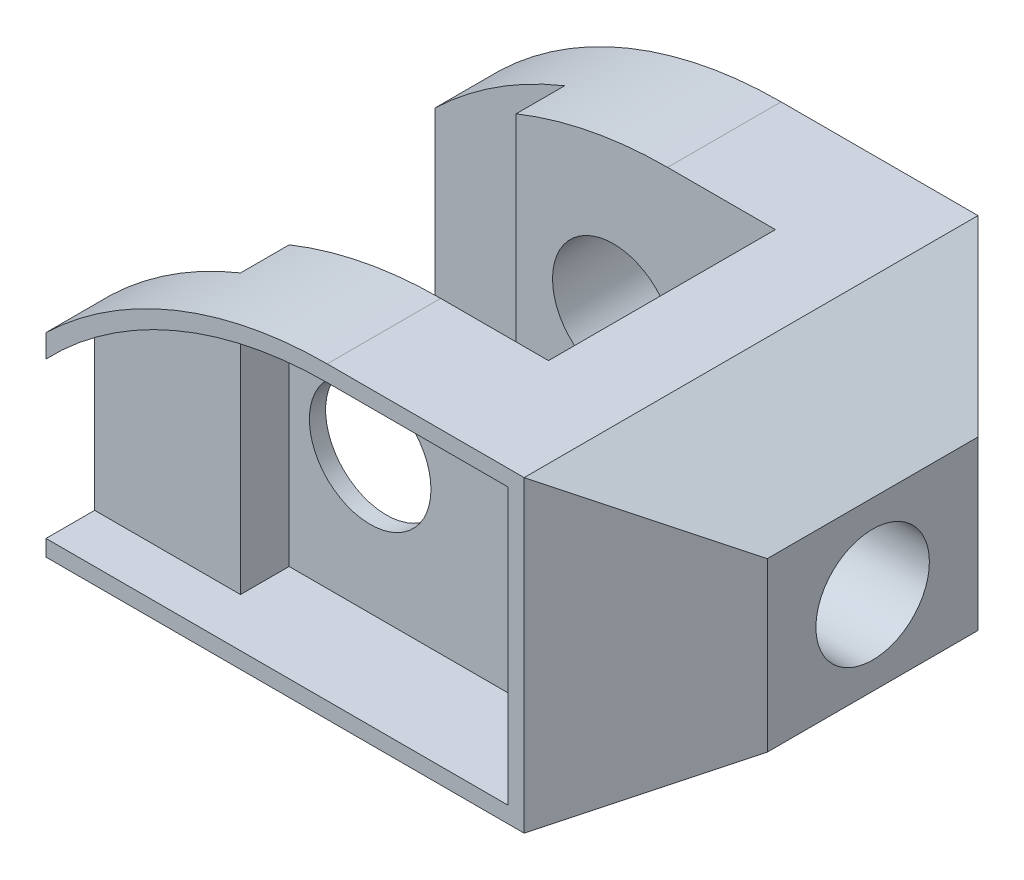
SolidWorks part; units mm, degrees
material "1060 Alloy"
ref_plane "Front Plane" through (0, 0, 0) normal (0, 0, 1) x (1, 0, 0)
ref_plane "Top Plane" through (0, 0, 0) normal (0, 1, 0) x (1, 0, 0)
ref_plane "Right Plane" through (0, 0, 0) normal (1, 0, 0) x (0, 0, -1)
sketch "Sketch1" plane through (0, 0, 0) normal (0, 0, 1) x (1, 0, 0)
  line L0 (-28, -19) -> (31, -19)
  line L1 (-28, -19) -> (-28, 5)
  line L2 (6.6987, 19) -> (31, 19)
  line L3 (0, 0) -> (0, 50000) construction
  line L4 (31, 19) -> (46, 10.3397)
  line L5 (31, -19) -> (46, -10.3397)
  line L6 (46, 10.3397) -> (46, -10.3397)
  line L7 (31, -19) -> (31, 49981) construction
  circle A0 centre (0, 0) radius 7.5
  arc A3 (6.6987, 19) -> (-28, 5) centre (6.6987, -31) ccw
  dimension "D1" = 15
  dimension "D6" = 50
  dimension "D2" = 19
  dimension "D3" = 31
  dimension "D4" = 59
  dimension "D5" = 24
  dimension "D7" = 38
  dimension "D8" = 30
  dimension "D9" = 15
  dimension "D10" = 30
extrude "Boss-Extrude1" add sketch "Sketch1" along normal blind 56
sketch "Sketch2" plane through (0, 19, 0) normal (0, 1, 0) x (1, 0, 0)
  line L0 (31, 0) -> (46, -15)
  line L1 (46, -56) -> (46, 0) construction
  line L2 (46, 0) -> (31, 0) construction
  line L3 (31, -56) -> (46, -41)
  line L4 (46, -56) -> (31, -56) construction
  line L5 (20, 0) -> (20, -56) construction
  line L6 (31, 0) -> (6.6987, 0) construction
  line L7 (31, -56) -> (6.6987, -56) construction
  line L8 (31, -56) -> (31, 0) construction
  line L9 (6.6987, -28) -> (-49993.3013, -28) construction
  line L10 (6.6987, -56) -> (6.6987, 0) construction
  line L11 (-28, 0) -> (-28, -8) construction
  line L12 (-28, -56) -> (-28, 0) construction
  line L13 (-28, -8) -> (-28, -14) construction
  line L14 (-28, -8) -> (-12, -8)
  line L15 (-12, -8) -> (-12, -14)
  line L16 (-12, -14) -> (20, -14)
  line L17 (20, -14) -> (20, -42)
  line L18 (-28, -8) -> (-28, -48)
  line L19 (-12, -42) -> (20, -42)
  line L20 (-12, -48) -> (-12, -42)
  line L21 (-28, -48) -> (-12, -48)
  line L22 (31, 0) -> (46, 0)
  line L23 (46, 0) -> (46, -15)
  line L24 (46, -41) -> (46, -56)
  line L25 (46, -56) -> (31, -56)
  point P24 (6.6987, -28)
  point P39 (20, -28)
  point P42 (-28, -28)
  dimension "D1" = 45
  dimension "D2" = 45
  dimension "D3" = 11
  dimension "D4" = 8
  dimension "D5" = 6
  dimension "D6" = 16
extrude "Cut-Extrude1" cut sketch "Sketch2" against normal up to surface (38 mm away) up to face at (1.5, -19, 28)
sketch "Sketch3" plane through (46, 0, 0) normal (1, 0, 0) x (0, 0, -1)
  line L0 (-56, -19) -> (-56, 19) construction
  line L1 (-56, -19) -> (0, -19) construction
  circle A0 centre (-28, 0) radius 7
  point P2 (-24.4457, -1.2399)
  dimension "D1" = 14
  dimension "D2" = 28
  dimension "D3" = 19
extrude "Cut-Extrude2" cut sketch "Sketch3" against normal up to surface (26 mm away) up to face at (20, 0, 28)
sketch "Sketch7" plane through (0, 0, 56) normal (0, 0, 1) x (1, 0, 0)
  line L0 (-28, 2.1662) -> (-28, -17)
  line L1 (-28, 5) -> (-28, -19) construction
  line L2 (-28, -19) -> (31, -19) construction
  line L3 (-28, -17) -> (29, -17)
  line L4 (31, -19) -> (31, 19) construction
  line L5 (29, -17) -> (29, 17)
  line L6 (31, 19) -> (6.6987, 19) construction
  line L7 (29, 17) -> (6.6987, 17)
  arc A0 (6.6987, 17) -> (-28, 2.1662) centre (6.6987, -31) ccw
  dimension "D4" = 48
  dimension "D1" = 2
  dimension "D2" = 2
  dimension "D3" = 2
extrude "Cut-Extrude3" cut sketch "Sketch7" against normal offset from surface (6 mm away) 2 up to face at (-20.1248, -4.2146, 48)
sketch "Sketch10" plane through (0, 0, 50) normal (0, 0, 1) x (1, 0, 0)
  line L0 (-28, -17) -> (-10, -17) construction
  line L1 (29, -17) -> (-28, -17) construction
  line L2 (-10, -17) -> (-10, 14.0017)
  line L3 (-10, -17) -> (29, -17)
  line L4 (29, -17) -> (29, 17)
  line L5 (29, 17) -> (6.6987, 17)
  arc A0 (6.6987, 17) -> (-28, 2.1662) centre (6.6987, -31) ccw construction
  arc A1 (6.6987, 17) -> (-10, 14.0017) centre (6.6987, -31) ccw
  dimension "D1" = 18
extrude "Cut-Extrude4" cut sketch "Sketch10" against normal offset from surface (6 mm away) 2 up to face at (7.5, 0, 42)
equation "\"A\"= 56"
equation "\"B\"= 38"
equation "\"C\"= 59"
equation "\"D4@Sketch1\"=\"C\""
equation "\"D7@Sketch1\"=\"B\""
equation "\"D1@Boss-Extrude1\"=\"A\""
equation "\"D2@Sketch3\"=\"A\"/2"
equation "\"D3@Sketch3\"=\"B\"/2"
